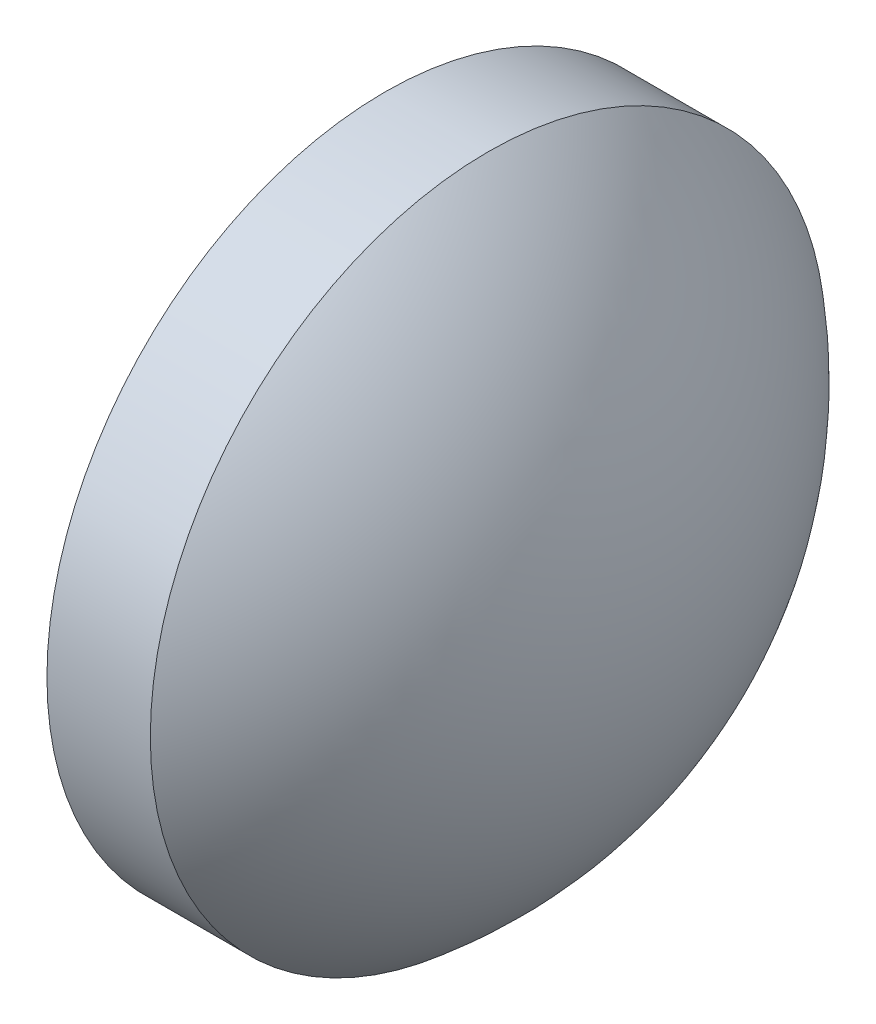
SolidWorks part; units mm, degrees
ref_plane "前视基准面" through (0, 0, 0) normal (0, 0, 1) x (1, 0, 0)
ref_plane "上视基准面" through (0, 0, 0) normal (0, 1, 0) x (1, 0, 0)
ref_plane "右视基准面" through (0, 0, 0) normal (1, 0, 0) x (0, 0, -1)
sketch "草图1" plane through (0, 0, 0) normal (0, 0, 1) x (1, 0, 0)
  line L0 (534.6781, 134.3762) -> (540.0564, 134.3762) construction
  line L1 (535.9096, 134.3762) -> (535.9096, 139.3762)
  line L2 (535.9096, 139.3762) -> (537.4396, 139.3762)
  line L3 (535.9096, 134.3762) -> (539.8096, 134.3762)
  arc A0 (539.8096, 134.3762) -> (537.4396, 139.3762) centre (533.3504, 134.3762) ccw
revolve "旋转1" add sketch "草图1" angle 360 about L0
